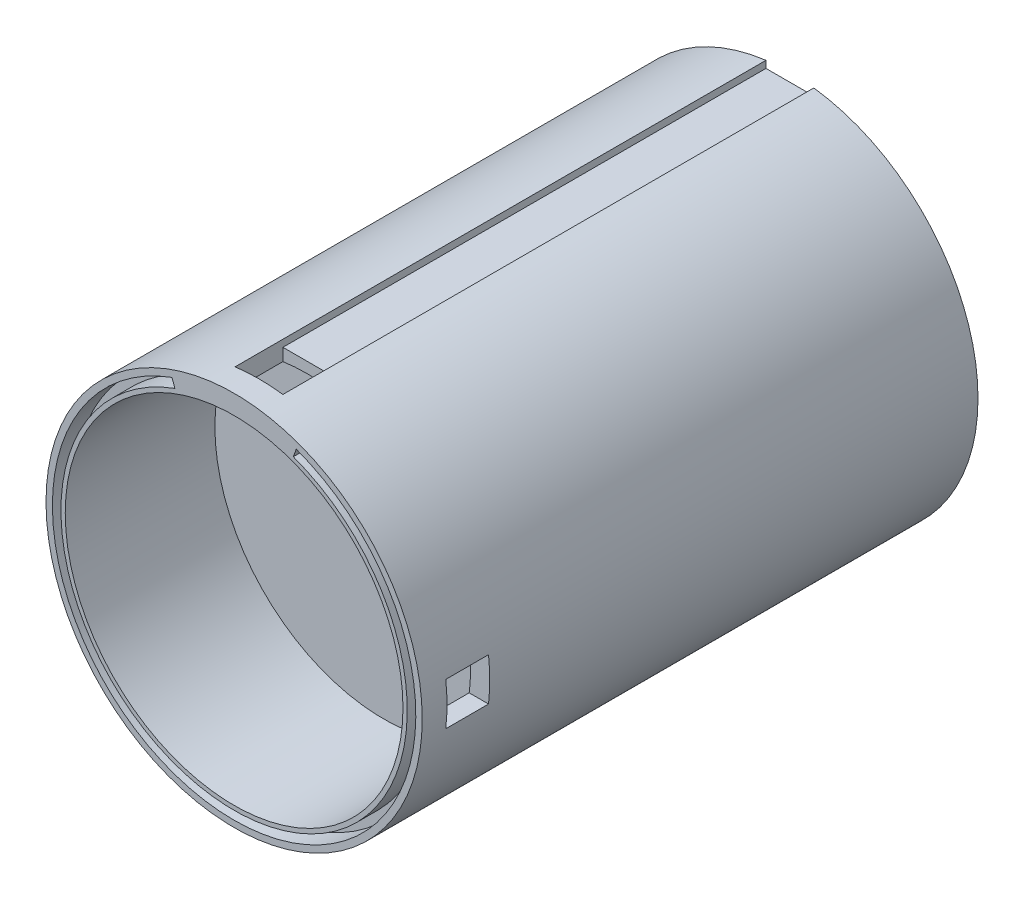
SolidWorks part; units mm, degrees
ref_plane "Front Plane" through (0, 0, 0) normal (0, 0, 1) x (1, 0, 0)
ref_plane "Top Plane" through (0, 0, 0) normal (0, 1, 0) x (1, 0, 0)
ref_plane "Right Plane" through (0, 0, 0) normal (1, 0, 0) x (0, 0, -1)
sketch "Sketch1" plane through (0, 0, 0) normal (0, 0, 1) x (1, 0, 0)
  circle A0 centre (0, 0) radius 44
  dimension "D1" = 88
extrude "Boss-Extrude1" add sketch "Sketch1" along normal blind 130 contours A0
sketch "Sketch2" plane through (0, 0, 0) normal (0, 0, -1) x (-1, 0, 0)
  circle A0 centre (0, 0) radius 39.5
  circle A1 centre (0, 0) radius 44 construction
  dimension "D1" = 79
extrude "Cut-Extrude1" cut sketch "Sketch2" against normal blind 90
sketch "Sketch3" plane through (0, 0, 130) normal (0, 0, 1) x (1, 0, 0)
  circle A0 centre (0, 0) radius 39.5
  circle A1 centre (0, 0) radius 44 construction
  dimension "D1" = 79
extrude "Cut-Extrude2" cut sketch "Sketch3" against normal blind 35
ref_plane "Plane1" through (0, 42, 0) normal (0, 1, 0) x (1, 0, 0)
sketch "Sketch6" plane through (0, 42, 0) normal (0, 1, 0) x (1, 0, 0)
  line L0 (0, 6.4486) -> (0, -145.0945) construction
  line L1 (-5.5966, -124.1784) -> (5.5966, -124.1784)
  line L2 (-5.5966, -124.1784) -> (-5.5966, 8.1784)
  line L3 (5.5966, -124.1784) -> (5.5966, 8.1784)
  line L4 (-5.5966, 8.1784) -> (5.5966, 8.1784)
  line L5 (-5.5966, -124.1784) -> (5.5966, 8.1784) construction
  line L6 (5.5966, -124.1784) -> (-5.5966, 8.1784) construction
  point P4 (0, -58)
  dimension "D1" = 5.5966
  dimension "D2" = 8.1784
  dimension "D3" = 58
extrude "Cut-Extrude3" cut sketch "Sketch6" along normal blind 95
sketch "Sketch7" plane through (0, 42, 0) normal (0, 1, 0) x (1, 0, 0)
  line L0 (0, -107.9351) -> (0, -126.4696) construction
  line L1 (5.5966, -124.1784) -> (5.5966, 0) construction
  line L2 (-5.5966, -124.1784) -> (5.5966, -124.1784)
  line L3 (-5.5966, -124.1784) -> (-5.5966, -112.9852)
  line L4 (-5.5966, -112.9852) -> (5.5966, -112.9852)
  line L5 (5.5966, -124.1784) -> (5.5966, -112.9852)
extrude "Cut-Extrude4" cut sketch "Sketch7" against normal blind 25
sketch "Sketch9" plane through (0, 0, 0) normal (0, 0, -1) x (-1, 0, 0)
  line L0 (14.5359, 39.9369) -> (13.8518, 38.0576)
  line L1 (0, 0) -> (14.5359, 39.9369) construction
  line L2 (0, 0) -> (0, 53.6445) construction
  line L3 (5.5966, 43.6426) -> (5.5966, 39.1015) construction
  line L4 (-5.5966, 43.6426) -> (-5.5966, 42) construction
  line L5 (-14.5359, 39.9369) -> (-13.8518, 38.0576)
  arc A0 (-14.5359, 39.9369) -> (14.5359, 39.9369) centre (0, 0) ccw
  arc A1 (-13.8518, 38.0576) -> (13.8518, 38.0576) centre (0, 0) ccw
  point P4 (13.8518, 38.0576)
  dimension "D1" = 81
  dimension "D2" = 85
  dimension "D3" = 20
extrude "Cut-Extrude5" cut sketch "Sketch9" against normal blind 5
ref_plane "Plane2" through (40, 0, 0) normal (1, 0, 0) x (0, 0, -1)
sketch "Sketch11" plane through (40, 0, 0) normal (1, 0, 0) x (0, 0, -1)
  line L0 (-135.7205, 0) -> (3.8947, 0) construction
  line L1 (-130, 44) -> (-130, -44) construction
  line L2 (-124.2, 5) -> (-114.2, 5)
  line L3 (-124.2, 5) -> (-124.2, -5)
  line L4 (-124.2, -5) -> (-114.2, -5)
  line L5 (-114.2, 5) -> (-114.2, -5)
  dimension "D1" = 10
  dimension "D2" = 10
  dimension "D3" = 5
  dimension "D4" = 5.8
extrude "Cut-Extrude6" cut sketch "Sketch11" along normal blind 5 and the other way blind 5
ref_plane "Plane3" through (0, 0, 65) normal (0, 0, -1) x (-1, 0, 0)
mirror "Mirror1" about plane through (0, 0, 65) normal (0, 0, -1) of "Cut-Extrude5"
